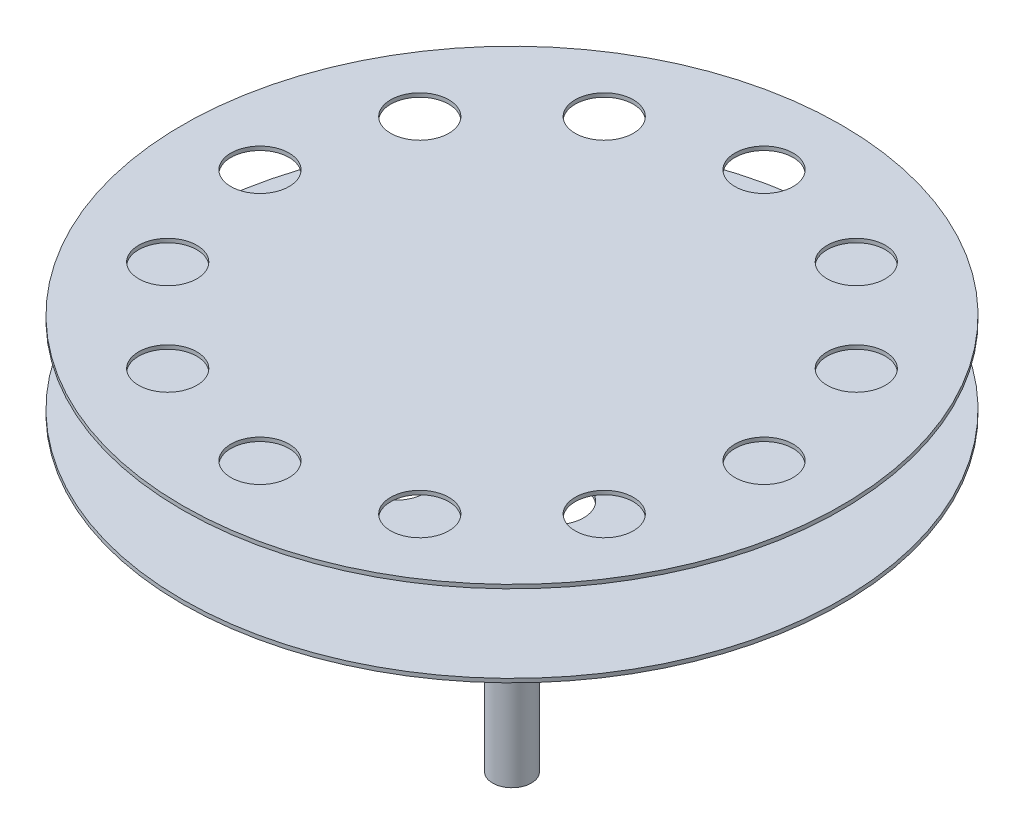
SolidWorks part; units mm, degrees
ref_plane "Front Plane" through (0, 0, 0) normal (0, 0, 1) x (1, 0, 0)
ref_plane "Top Plane" through (0, 0, 0) normal (0, 1, 0) x (1, 0, 0)
ref_plane "Right Plane" through (0, 0, 0) normal (1, 0, 0) x (0, 0, -1)
sketch "Sketch1" plane through (0, 0, 0) normal (0, 0, 1) x (1, 0, 0)
  line L0 (0, 0) -> (0, 52.2611) construction
  line L1 (0, 102) -> (-84.9998, 102)
  line L2 (-84.9998, 102) -> (-84.9998, 101)
  line L3 (-84.9998, 101) -> (-5, 101)
  line L4 (-5, 101) -> (-5, 81)
  line L5 (-5, 81) -> (-84.9998, 81)
  line L6 (-84.9998, 81) -> (-84.9998, 80)
  line L7 (-84.9998, 80) -> (-5, 80)
  line L8 (-5, 80) -> (-5, 0)
  line L9 (-5, 0) -> (0, 0)
  line L10 (0, 0) -> (0, 102)
  line L11 (-5, 81) -> (-5, 80) construction
  line L12 (-84.9998, 101) -> (-84.9998, 81) construction
  dimension "D1" = 84.9998
  dimension "D2" = 1
  dimension "D3" = 20
  dimension "D4" = 5
  dimension "D5" = 80
ref_axis "Axis1" through (0, 54.8742, 0) along (0, -1, 0)
revolve "Revolve1" add sketch "Sketch1" angle 360 about axis through (0, 54.8742, 0) along (0, -1, 0)
sketch "Sketch2" plane through (0, 102, 0) normal (0, 1, 0) x (1, 0, 0)
  line L0 (0, 0) -> (0, 65) construction
  circle A0 centre (0, 65) radius 7.5
  dimension "D1" = 15
  dimension "D2" = 65
extrude "Cut-Extrude1" cut sketch "Sketch2" against normal blind 2
pattern_circular "CirPattern1" count 12 over 360 about axis through (0, 0, 0) along (0, 1, 0) of "Cut-Extrude1"
sketch "Sketch3" plane through (0, 80, 0) normal (0, -1, 0) x (1, 0, 0)
  line L0 (0, 0) -> (0, 30) construction
  circle A0 centre (0, 30) radius 7.5
  dimension "D2" = 15
  dimension "D1" = 30
extrude "Cut-Extrude2" cut sketch "Sketch3" against normal blind 2
pattern_circular "CirPattern2" count 6 over 360 about axis through (0, 0, 0) along (0, 1, 0) of "Cut-Extrude2"
equation "\"TubeDiameter\" = 6.6929in"
equation "\"D1@Sketch1\"=\"TubeDiameter\"/2"
